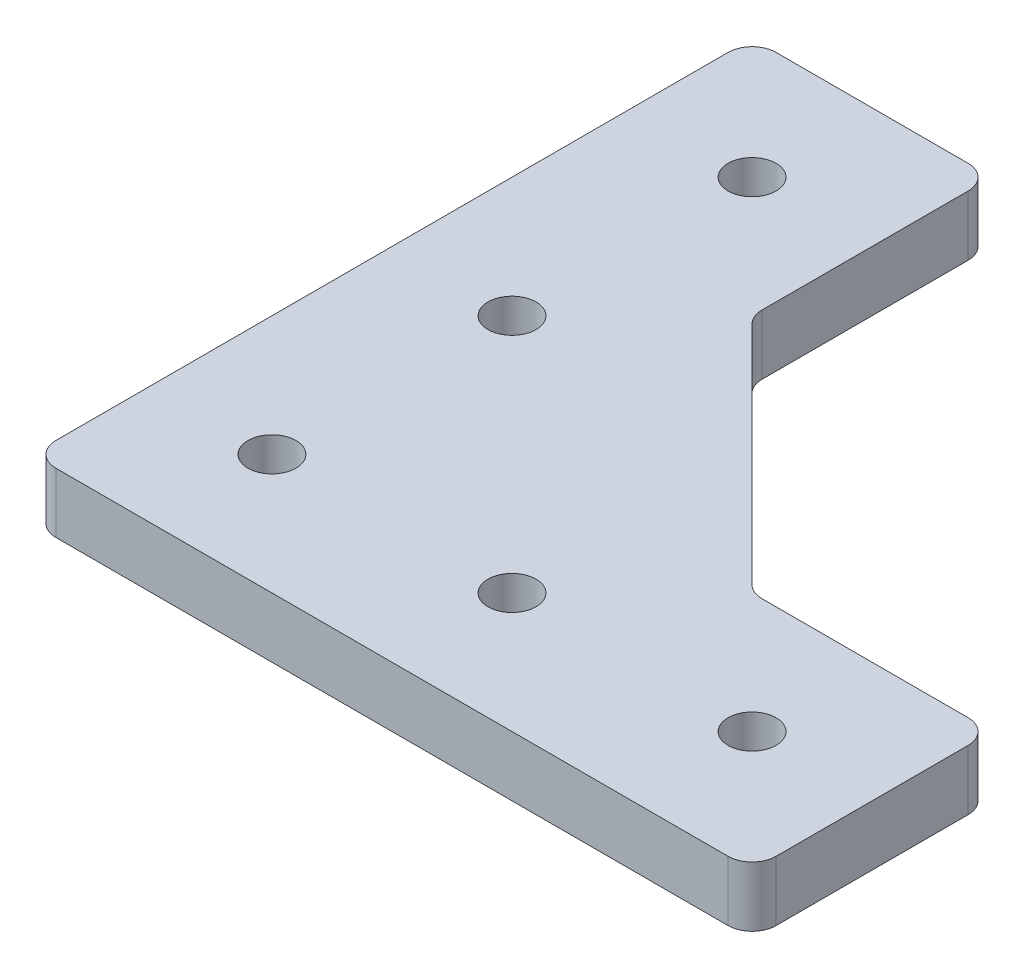
SolidWorks part; units mm, degrees
ref_plane "前视基准面" through (0, 0, 0) normal (0, 0, 1) x (1, 0, 0)
ref_plane "上视基准面" through (0, 0, 0) normal (0, 1, 0) x (1, 0, 0)
ref_plane "右视基准面" through (0, 0, 0) normal (1, 0, 0) x (0, 0, -1)
sketch "Sketch1" plane through (0, 0, 0) normal (0, 1, 0) x (1, 0, 0)
  line L0 (0, 0) -> (0, 40) construction
  line L1 (0, 0) -> (40, 0) construction
  line L3 (-10, 50) -> (10, 50)
  line L4 (-10, 50) -> (-10, -10)
  line L5 (-10, -10) -> (10, -10)
  line L6 (10, 50) -> (10, -10)
  line L7 (-10, 50) -> (10, -10) construction
  line L8 (-10, -10) -> (10, 50) construction
  line L9 (50, 10) -> (-10, 10)
  line L10 (50, 10) -> (50, -10)
  line L11 (50, -10) -> (-10, -10)
  line L12 (-10, 10) -> (-10, -10)
  line L13 (50, 10) -> (-10, -10) construction
  line L14 (50, -10) -> (-10, 10) construction
  circle A0 centre (0, 0) radius 2
  circle A1 centre (40, 0) radius 2
  circle A2 centre (0, 40) radius 2
  circle A3 centre (20, 0) radius 2
  circle A4 centre (0, 20) radius 2
  dimension "D1" = 20
  dimension "D2" = 4
  dimension "D3" = 20
  dimension "D4" = 20
  dimension "D5" = 20
  dimension "D6" = 20
  dimension "D7" = 20
extrude "Boss-Extrude1" add sketch "Sketch1" along normal blind 5 contours L11 L10 L9 L6 A3 A1 | L6 L9 L4 L5 A0 | L9 L6 L3 L4 A4 A2
fillet "Fillet1" radius 2 6 edges at (50, 2.5, -10) (10, 2.5, -10) (-10, 2.5, 10) (-10, 2.5, -50) (50, 2.5, 10) (10, 2.5, -50)
sketch "Sketch2" plane through (0, 5, 0) normal (0, 1, 0) x (1, 0, 0)
  line L0 (10, 30) -> (30, 10)
  line L1 (10, 48) -> (10, 12) construction
  line L2 (48, 10) -> (12, 10) construction
  line L3 (30, 10) -> (7.0503, 7.0503)
  line L4 (7.0503, 7.0503) -> (10, 30)
  line L5 (10.5858, 10.5858) -> (-9.4142, -9.4142) construction
  arc A0 (10, 12) -> (12, 10) centre (12, 12) ccw construction
  arc A1 (-10, -8) -> (-8, -10) centre (-8, -8) ccw construction
  dimension "D1" = 5
extrude "Boss-Extrude2" add sketch "Sketch2" against normal blind 5
fillet "Fillet2" radius 2 2 edges at (30, 2.5, -10) (10, 2.5, -30)
